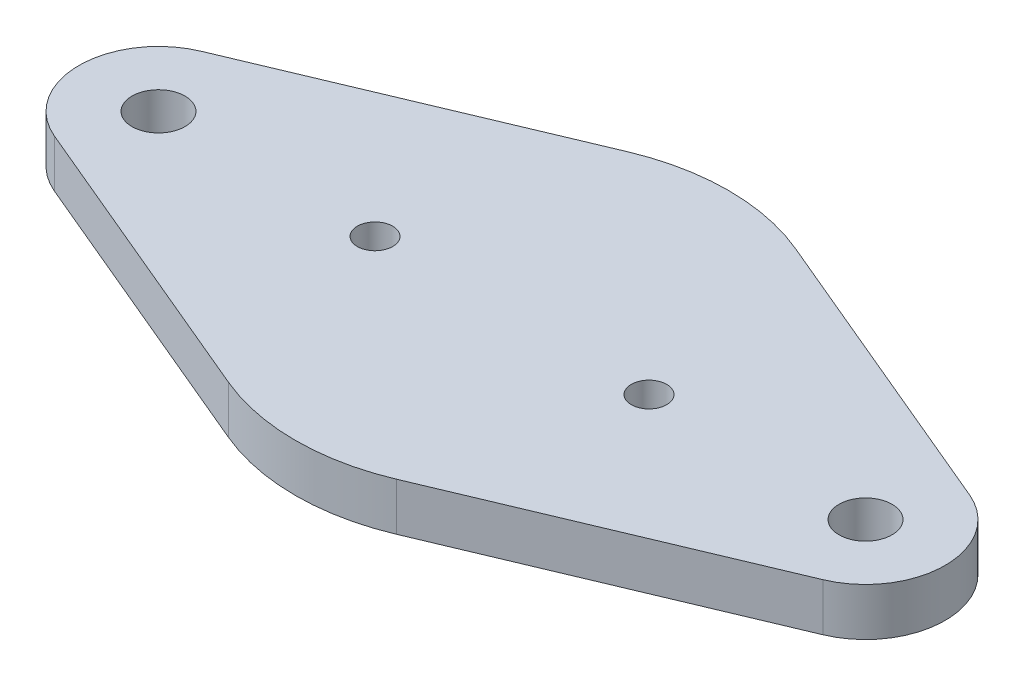
SolidWorks part; units mm, degrees
material "ABS PC"
ref_plane "Front Plane" through (0, 0, 0) normal (0, 0, 1) x (1, 0, 0)
ref_plane "Top Plane" through (0, 0, 0) normal (0, 1, 0) x (1, 0, 0)
ref_plane "Right Plane" through (0, 0, 0) normal (1, 0, 0) x (0, 0, -1)
sketch "Sketch1" plane through (0, 0, 0) normal (0, 1, 0) x (1, 0, 0)
  line L0 (4.7469, 11.2929) -> (21.7437, 4.1484)
  line L1 (21.7437, -4.1484) -> (4.7469, -11.2929)
  line L2 (-4.7469, 11.2929) -> (-21.7437, 4.1484)
  line L3 (-21.7437, -4.1484) -> (-4.7469, -11.2929)
  arc A0 (-4.7469, -11.2929) -> (4.7469, -11.2929) centre (0, 0) ccw
  arc A1 (21.7437, -4.1484) -> (21.7437, 4.1484) centre (20, 0) ccw
  arc A2 (-21.7437, 4.1484) -> (-21.7437, -4.1484) centre (-20, 0) ccw
  arc A3 (4.7469, 11.2929) -> (-4.7469, 11.2929) centre (0, 0) ccw
  dimension "D1" = 24.5
  dimension "D2" = 9
  dimension "D3" = 9
  dimension "D4" = 20
  dimension "D5" = 20
extrude "Boss-Extrude1" add sketch "Sketch1" along normal blind 2.7
sketch "Sketch2" plane through (0, 2.7, 0) normal (0, 1, 0) x (1, 0, 0)
  circle A0 centre (-20, 0) radius 1.5
  circle A1 centre (20, 0) radius 1.5
  circle A2 centre (7.75, 0) radius 1
  circle A3 centre (-7.75, 0) radius 1
  dimension "D1" = 3
  dimension "D2" = 3
  dimension "D3" = 2
  dimension "D4" = 2
  dimension "D5" = 7.75
  dimension "D6" = 7.75
extrude "Cut-Extrude1" cut sketch "Sketch2" against normal up to next
